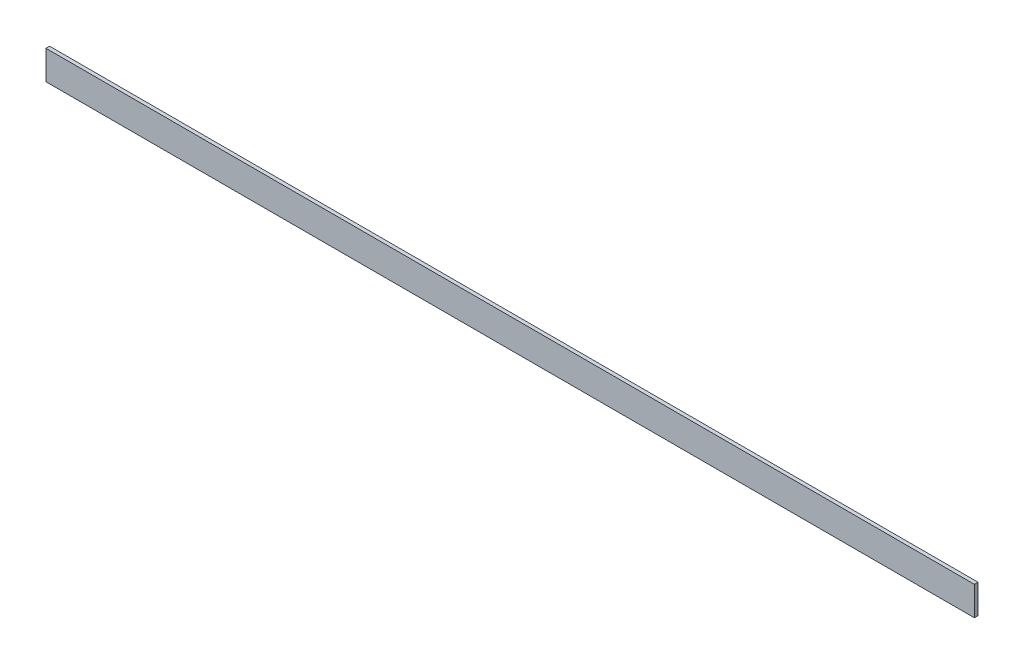
SolidWorks part; units mm, degrees
material "PC High Viscosity"
ref_plane "Front Plane" through (0, 0, 0) normal (0, 0, 1) x (1, 0, 0)
ref_plane "Top Plane" through (0, 0, 0) normal (0, 1, 0) x (1, 0, 0)
ref_plane "Right Plane" through (0, 0, 0) normal (1, 0, 0) x (0, 0, -1)
sketch "Sketch1" plane through (0, 0, 0) normal (0, 1, 0) x (1, 0, 0)
  line L1 (0, 0) -> (406.4, 0)
  line L2 (0, 0) -> (0, 1.5875)
  line L3 (0, 1.5875) -> (406.4, 1.5875)
  line L4 (406.4, 0) -> (406.4, 1.5875)
  dimension "D1" = 406.4
  dimension "D2" = 1.5875
extrude "Boss-Extrude1" add sketch "Sketch1" along normal blind 12.7
